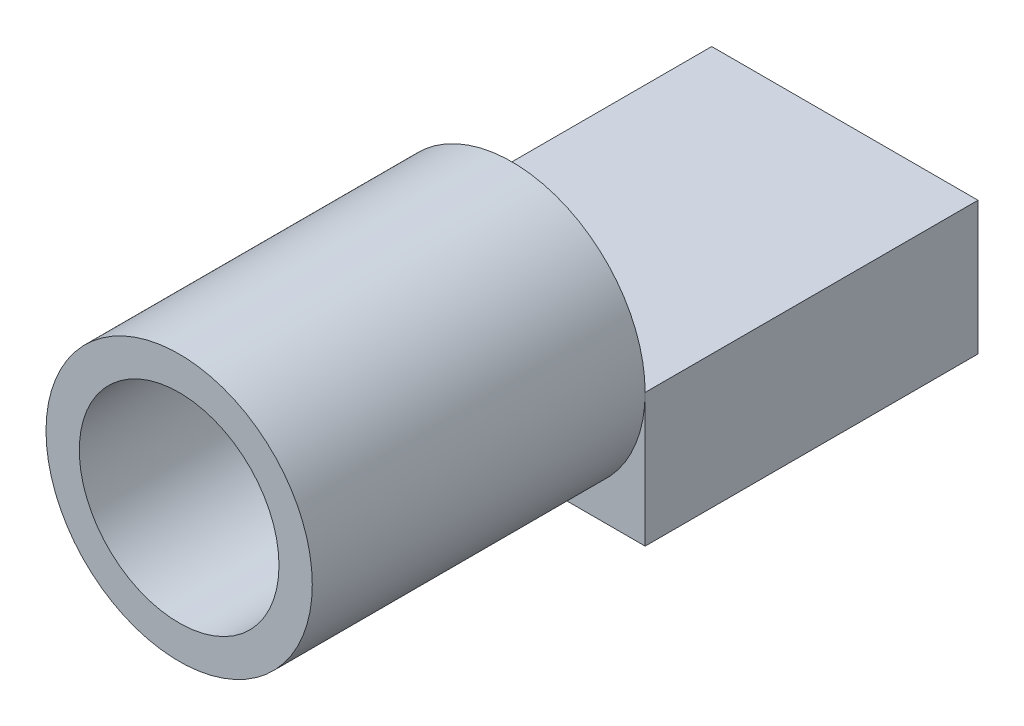
SolidWorks part; units mm, degrees
ref_plane "Plano frontal" through (0, 0, 0) normal (0, 0, 1) x (1, 0, 0)
ref_plane "Plano superior" through (0, 0, 0) normal (0, 1, 0) x (1, 0, 0)
ref_plane "Plano direito" through (0, 0, 0) normal (1, 0, 0) x (0, 0, -1)
sketch "Esboço1" plane through (0, 0, 0) normal (0, 0, 1) x (1, 0, 0)
  circle A0 centre (0, 0) radius 4
  circle A1 centre (0, 0) radius 3
  dimension "D1" = 6
  dimension "D2" = 8
extrude "Ressalto-extrusão1" add sketch "Esboço1" along normal blind 10
sketch "Esboço2" plane through (0, 0, 0) normal (0, 0, -1) x (-1, 0, 0)
  line L0 (-4, 0) -> (4, 0)
  line L1 (4, 0) -> (4, -4)
  line L2 (4, -4) -> (-4, -4)
  line L3 (-4, -4) -> (-4, 0)
  circle A0 centre (0, 0) radius 4 construction
extrude "Ressalto-extrusão2" add sketch "Esboço2" along normal blind 10
